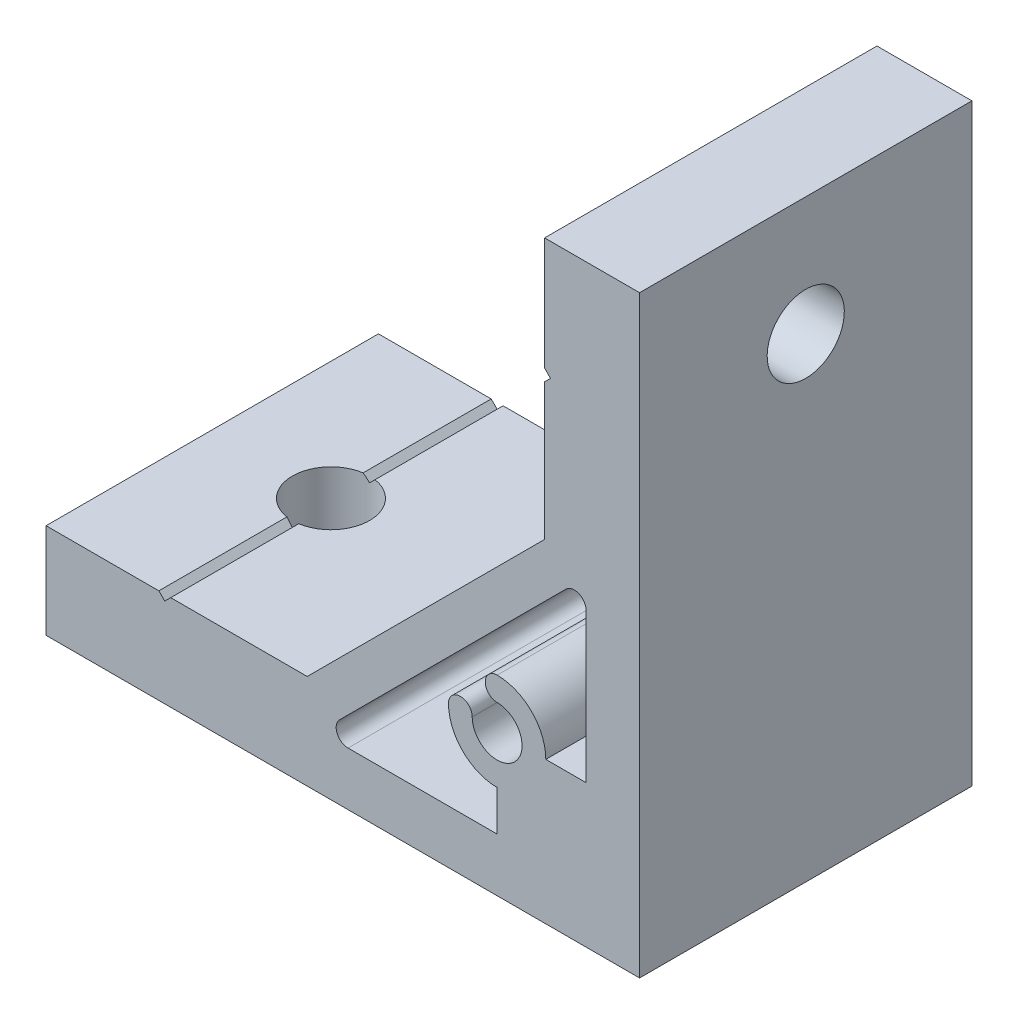
SolidWorks part; units mm, degrees
material "6063 T5"
ref_plane "Спереди" through (0, 0, 0) normal (0, 0, 1) x (1, 0, 0)
ref_plane "Сверху" through (0, 0, 0) normal (0, 1, 0) x (1, 0, 0)
ref_plane "Справа" through (0, 0, 0) normal (1, 0, 0) x (0, 0, -1)
sketch "Эскиз1" plane through (0, 0, 0) normal (0, 0, 1) x (1, 0, 0)
  line L0 (-50, 0) -> (0, 0)
  line L1 (0, 0) -> (0, 50)
  line L2 (0, 50) -> (-8, 50)
  line L3 (-8, 50) -> (-8, 40.5)
  line L4 (-8, 40.5) -> (-7.5, 40)
  line L5 (-7.5, 40) -> (-8, 39.5)
  line L6 (-8, 39.5) -> (-8, 28)
  line L7 (-8, 28) -> (-28, 8)
  line L8 (-28, 8) -> (-39.5, 8)
  line L9 (-39.5, 8) -> (-40, 7.5)
  line L10 (-40, 7.5) -> (-40.5, 8)
  line L11 (-40.5, 8) -> (-50, 8)
  line L12 (-50, 8) -> (-50, 0)
  line L13 (-4.5, 12) -> (-4.5, 24.5603)
  line L14 (-6.2071, 25.2674) -> (-25.2674, 6.2071)
  line L15 (-24.5603, 4.5) -> (-12, 4.5)
  line L16 (-12, 4.5) -> (-12, 7.9)
  line L17 (-7.9, 12) -> (-4.5, 12)
  arc A0 (-4.5, 24.5603) -> (-6.2071, 25.2674) centre (-5.5, 24.5603) ccw
  arc A1 (-25.2674, 6.2071) -> (-24.5603, 4.5) centre (-24.5603, 5.5) ccw
  arc A2 (-12, 7.9) -> (-16.1, 12) centre (-12, 12) cw
  arc A3 (-16.1, 12) -> (-14.1, 12) centre (-15.1, 12) cw
  arc A4 (-14.1, 12) -> (-12, 14.1) centre (-12, 12) ccw
  arc A5 (-12, 14.1) -> (-12, 16.1) centre (-12, 15.1) cw
  arc A6 (-12, 16.1) -> (-7.9, 12) centre (-12, 12) cw
  dimension "D6" = 4.2
  dimension "D7" = 1
  dimension "D9" = 1
  dimension "D1" = 50
  dimension "D2" = 8
  dimension "D3" = 135
  dimension "D4" = 12
  dimension "D5" = 12
  dimension "D8" = 28
  dimension "D10" = 3.2
  dimension "D11" = 4.5
  dimension "D12" = 40
  dimension "D13" = 1
extrude "Бобышка-Вытянуть1" add sketch "Эскиз1" along normal mid plane 28
sketch "Эскиз2" plane through (-8, 0, 0) normal (-1, 0, 0) x (0, 0, 1)
  line L0 (14, 40) -> (-14, 40) construction
  circle A0 centre (0, 40) radius 3.25
  dimension "D1" = 6.5
extrude "Вырез-Вытянуть1" cut sketch "Эскиз2" against normal through all
sketch "Эскиз3" plane through (0, 8, 0) normal (0, 1, 0) x (1, 0, 0)
  line L0 (-40, -14) -> (-40, 14) construction
  circle A0 centre (-40, 0) radius 3.25
  dimension "D1" = 6.5
extrude "Вырез-Вытянуть2" cut sketch "Эскиз3" against normal through all
